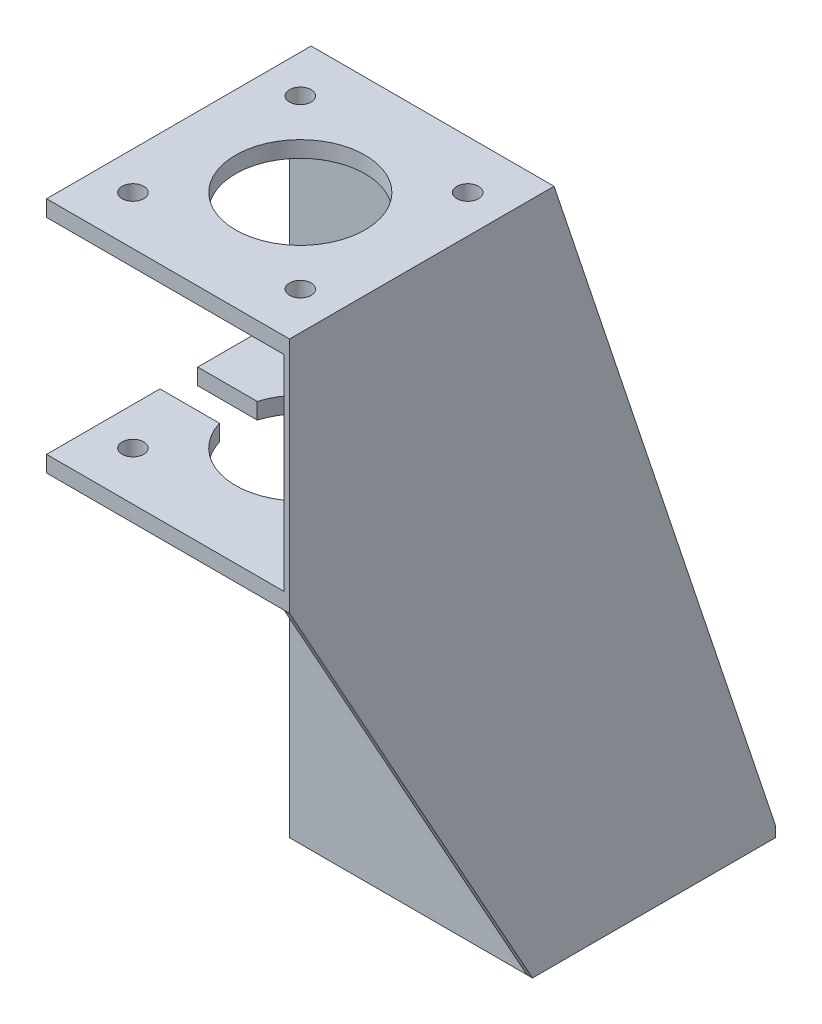
SolidWorks part; units mm, degrees
ref_plane "Alzado" through (0, 0, 0) normal (0, 0, 1) x (1, 0, 0)
ref_plane "Planta" through (0, 0, 0) normal (0, 1, 0) x (1, 0, 0)
ref_plane "Vista lateral" through (0, 0, 0) normal (1, 0, 0) x (0, 0, -1)
sketch "Croquis1" plane through (0, 0, 0) normal (0, 1, 0) x (1, 0, 0)
  line L1 (-22.5, 22.5) -> (22.5, 22.5)
  line L2 (-22.5, 22.5) -> (-22.5, -22.5)
  line L3 (-22.5, -22.5) -> (22.5, -22.5)
  line L4 (22.5, 22.5) -> (22.5, -22.5)
  line L5 (-22.5, 22.5) -> (22.5, -22.5) construction
  line L6 (-22.5, -22.5) -> (22.5, 22.5) construction
  point P0 (0, 0)
  dimension "D1" = 45
  dimension "D2" = 45
extrude "Saliente-Extruir1" add sketch "Croquis1" along normal blind 2
sketch "Croquis2" plane through (0, 2, 0) normal (0, 1, 0) x (1, 0, 0)
  line L0 (0, -18.5) -> (0, 22.5) construction
  line L1 (22.5, 22.5) -> (-22.5, 22.5) construction
  line L2 (-22.5, -22.5) -> (22.5, -22.5) construction
  line L3 (-15, -14.6921) -> (-15, 15.3079) construction
  line L4 (-18, -14.6921) -> (-18, 15.3079)
  line L5 (-12, -14.6921) -> (-12, 15.3079)
  line L6 (15, -14.6921) -> (15, 15.3079) construction
  line L7 (18, -14.6921) -> (18, 15.3079)
  line L8 (12, -14.6921) -> (12, 15.3079)
  arc A0 (-18, -14.6921) -> (-12, -14.6921) centre (-15, -14.6921) ccw
  arc A1 (-12, 15.3079) -> (-18, 15.3079) centre (-15, 15.3079) ccw
  arc A2 (18, -14.6921) -> (12, -14.6921) centre (15, -14.6921) cw
  arc A3 (12, 15.3079) -> (18, 15.3079) centre (15, 15.3079) cw
  point P4 (0, -22.5)
  point P9 (-15, 0.3079)
  point P16 (15, 0.3079)
  dimension "D3" = 3
  dimension "D1" = 4
  dimension "D2" = 30
  dimension "D4" = 15
extrude "Cortar-Extruir1" cut sketch "Croquis2" against normal blind 2
sketch "Croquis3" plane through (0, 2, 0) normal (0, 1, 0) x (1, 0, 0)
  line L0 (22.5, -22.5) -> (22.5, 22.5) construction
  line L1 (-22.5, -22.5) -> (22.5, -22.5)
  line L2 (-22.5, -22.5) -> (-22.5, -18.5)
  line L3 (-22.5, -18.5) -> (22.5, -18.5)
  line L4 (22.5, -22.5) -> (22.5, -18.5)
  dimension "D1" = 4
extrude "Saliente-Extruir2" add sketch "Croquis3" along normal blind 120
sketch "Croquis4" plane through (0, 122, 0) normal (0, 1, 0) x (1, 0, 0)
  line L4 (-22.5, -18.5) -> (-22.5, -22.5)
  line L5 (-22.5, -22.5) -> (22.5, -22.5)
  line L6 (22.5, -22.5) -> (22.5, -18.5)
  line L7 (22.5, -18.5) -> (-22.5, -18.5)
  line L8 (-22.5, -18.5) -> (-22.5, -22.5)
  line L9 (-22.5, -22.5) -> (22.5, -22.5)
  line L10 (22.5, -22.5) -> (22.5, -18.5)
  line L11 (22.5, -18.5) -> (-22.5, -18.5)
  dimension "D1" = 0
extrude "Saliente-Extruir3" add sketch "Croquis4" along normal blind 3
sketch "Croquis5" plane through (0, 0, 22.5) normal (0, 0, 1) x (1, 0, 0)
  line L0 (22.5, 125) -> (22.5, 0) construction
  line L1 (-22.5, 125) -> (22.5, 125)
  line L2 (-22.5, 125) -> (-22.5, 122)
  line L3 (-22.5, 122) -> (22.5, 122)
  line L4 (22.5, 125) -> (22.5, 122)
  dimension "D1" = 3
extrude "Saliente-Extruir4" add sketch "Croquis5" along normal blind 45
sketch "Croquis6" plane through (0, 125, 0) normal (0, 1, 0) x (1, 0, 0)
  line L0 (-22.5, -67.5) -> (22.5, -18.5) construction
  line L2 (-15.5, -27.5) -> (15.5, -27.5)
  line L3 (-15.5, -27.5) -> (-15.5, -58.5)
  line L4 (-15.5, -58.5) -> (15.5, -58.5)
  line L5 (15.5, -27.5) -> (15.5, -58.5)
  line L6 (-15.5, -27.5) -> (15.5, -58.5) construction
  line L7 (-15.5, -58.5) -> (15.5, -27.5) construction
  circle A0 centre (0, -43) radius 12
  circle A1 centre (-15.5, -27.5) radius 2
  circle A2 centre (15.5, -27.5) radius 2
  circle A3 centre (15.5, -58.5) radius 2
  circle A4 centre (-15.5, -58.5) radius 2
  point P4 (0, -43)
  dimension "D3" = 24
  dimension "D4" = 4
  dimension "D1" = 31
  dimension "D2" = 31
extrude "Cortar-Extruir2" cut sketch "Croquis6" against normal up to surface (3 mm away) contours A1 | A4 | A0 | A3 | A2 up to face at (-5.625, 122, 56.25)
sketch "Croquis7" plane through (0, 0, 22.5) normal (0, 0, 1) x (1, 0, 0)
  line L0 (-22.5, 122) -> (-22.5, 0) construction
  line L1 (-22.5, 84) -> (22.5, 84)
  line L2 (-22.5, 84) -> (-22.5, 81)
  line L3 (-22.5, 81) -> (22.5, 81)
  line L4 (22.5, 84) -> (22.5, 81)
  line L5 (22.5, 122) -> (22.5, 0) construction
  line L6 (-22.5, 122) -> (22.5, 122) construction
  dimension "D1" = 3
  dimension "D2" = 38
extrude "Saliente-Extruir5" add sketch "Croquis7" along normal blind 45
sketch "Croquis8" plane through (0, 125, 0) normal (0, 1, 0) x (1, 0, 0)
  circle A0 centre (0, -43) radius 12
  circle A1 centre (15.5, -58.5) radius 2
  circle A2 centre (15.5, -27.5) radius 2
  circle A3 centre (-15.5, -27.5) radius 2
  circle A4 centre (-15.5, -58.5) radius 2
extrude "Cortar-Extruir4" cut sketch "Croquis8" against normal up to surface (44 mm away) up to face at (0, 81, 45)
sketch "Croquis11" plane through (0, 84, 0) normal (0, 1, 0) x (1, 0, 0)
  line L0 (-22.5, -45.8101) -> (22.5, -45) construction
  line L1 (-22.5, -67.5) -> (-22.5, -22.5) construction
  line L2 (22.5, -67.5) -> (22.5, -22.5) construction
  line L3 (-12, -43) -> (-22.5, -43)
  line L5 (-36.4498, -39.5) -> (-8.5502, -39.5)
  line L6 (-36.4498, -39.5) -> (-36.4498, -46.5)
  line L7 (-36.4498, -46.5) -> (-8.5502, -46.5)
  line L8 (-8.5502, -39.5) -> (-8.5502, -46.5)
  line L9 (-36.4498, -39.5) -> (-8.5502, -46.5) construction
  line L10 (-36.4498, -46.5) -> (-8.5502, -39.5) construction
  circle A0 centre (0, -43) radius 12 construction
  dimension "D1" = 7
extrude "Cortar-Extruir5" cut sketch "Croquis11" against normal blind 45 contours L7 L8 L5 L6
sketch "Croquis14" plane through (22.5, 0, 0) normal (1, 0, 0) x (0, 0, -1)
  line L0 (-67.5, 122) -> (-67.5, 84)
  line L1 (-67.5, 84) -> (-18.5, 84)
  line L2 (-18.5, 125) -> (-18.5, 2) construction
  line L3 (-18.5, 84) -> (-18.5, 125)
  line L4 (-18.5, 125) -> (-67.5, 125)
  line L5 (-67.5, 125) -> (-67.5, 122)
extrude "Saliente-Extruir6" add sketch "Croquis14" against normal blind 1
sketch "Croquis16" plane through (22.5, 0, 0) normal (1, 0, 0) x (0, 0, -1)
  line L0 (-18.5, 125) -> (22.5, 2)
  line L1 (22.5, 2) -> (22.5, 0)
  line L2 (-22.5, 0) -> (22.5, 0) construction
  line L3 (22.5, 2) -> (22.5, 0) construction
  line L4 (22.5, 0) -> (-22.5, 0)
  line L5 (-22.5, 0) -> (-22.5, 125)
  line L6 (-67.5, 125) -> (-18.5, 125) construction
  line L7 (-22.5, 125) -> (-18.5, 125)
extrude "Saliente-Extruir7" add sketch "Croquis16" against normal blind 1
sketch "Croquis17" plane through (22.5, 0, 0) normal (1, 0, 0) x (0, 0, -1)
  line L0 (-67.5, 81) -> (-22.5, 0)
  line L2 (-22.5, 0) -> (-22.5, 84)
  line L3 (-22.5, 84) -> (-67.5, 84)
  line L4 (-67.5, 84) -> (-67.5, 81)
  line L5 (-22.5, 0) -> (22.5, 0) construction
extrude "Saliente-Extruir8" add sketch "Croquis17" against normal blind 1
